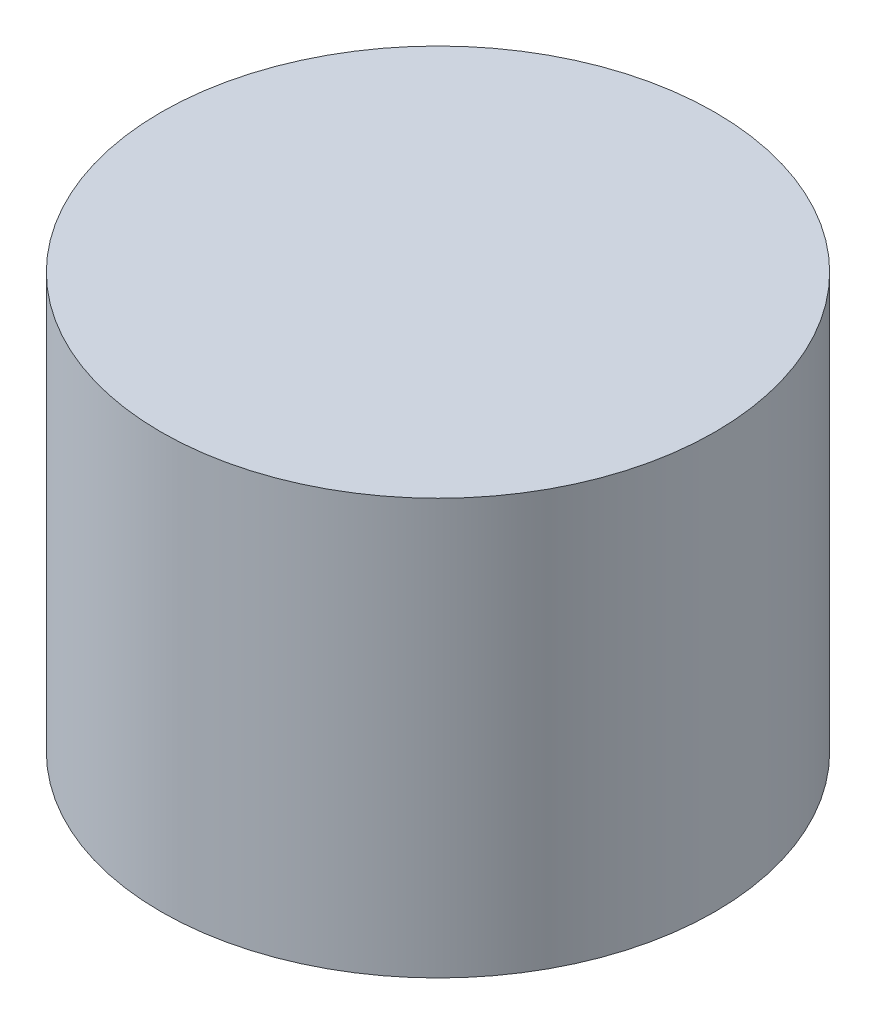
SolidWorks part; units mm, degrees
ref_plane "Front Plane" through (0, 0, 0) normal (0, 0, 1) x (1, 0, 0)
ref_plane "Top Plane" through (0, 0, 0) normal (0, 1, 0) x (1, 0, 0)
ref_plane "Right Plane" through (0, 0, 0) normal (1, 0, 0) x (0, 0, -1)
sketch "Sketch1" plane through (0, 0, 0) normal (0, 1, 0) x (1, 0, 0)
  circle A0 centre (0, 0) radius 4
extrude "Boss-Extrude1" add sketch "Sketch1" along normal blind 6
